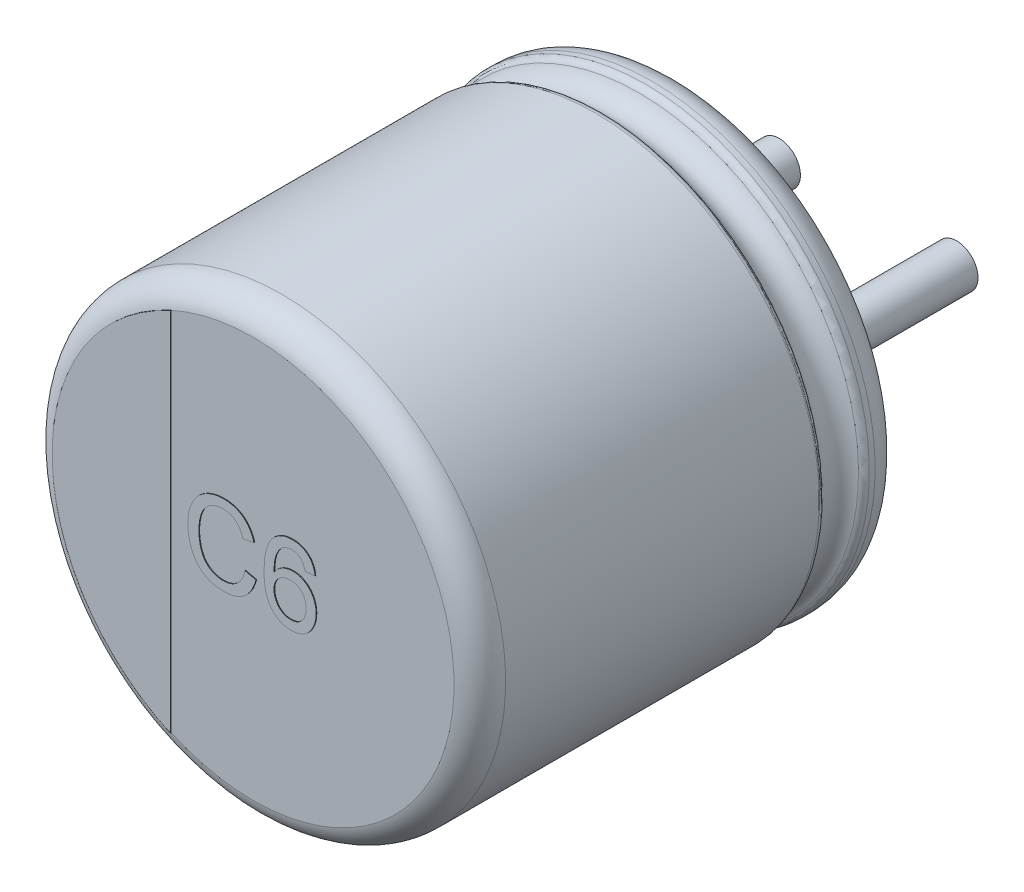
SolidWorks part; units mm, degrees
ref_plane "Plan de face" through (0, 0, 0) normal (0, 0, 1) x (1, 0, 0)
ref_plane "Plan de dessus" through (0, 0, 0) normal (0, 1, 0) x (1, 0, 0)
ref_plane "Plan de droite" through (0, 0, 0) normal (1, 0, 0) x (0, 0, -1)
sketch "Sketch10" plane through (0, 0, 0) normal (1, 0, 0) x (0, 0, -1)
  line L0 (18.1631, 0) -> (-18.9631, 0) construction
  line L1 (-6, 0) -> (-0.05, 0)
  line L2 (-6, 0) -> (-6, 2.8236)
  line L3 (-5.6, 3.15) -> (-1.1846, 3.15)
  line L4 (-0.05, 2.5531) -> (-0.05, 0)
  line L7 (-0.4794, 3.15) -> (-0.3982, 3.15)
  arc A0 (-6, 2.8236) -> (-5.6, 3.15) centre (-5.6068, 2.7501) cw
  arc A1 (-0.3982, 3.15) -> (-0.05, 2.5531) centre (-0.3982, 2.75) cw
  arc A2 (-0.5713, 3.0894) -> (-1.0926, 3.0894) centre (-0.832, 3.201) cw
  arc A3 (-1.0926, 3.0894) -> (-1.1846, 3.15) centre (-1.1846, 3.05) ccw
  arc A4 (-0.5713, 3.0894) -> (-0.4794, 3.15) centre (-0.4794, 3.05) cw
  point P4 (0.57, 0)
  point P13 (-6, 3.15)
  dimension "D2" = 0.4
  dimension "D3" = 0.4
  dimension "D4" = 0.1
  dimension "D5" = 0.1
  dimension "D1" = 3.15
  dimension "D7" = 0.05
  dimension "D8" = 3.15
revolve "Повернуть1" add sketch "Sketch10" angle 360 about L0
sketch "Эскиз2" plane through (0, 0, 0.05) normal (0, 0, -1) x (-1, 0, 0)
  line L1 (0, 0.7993) -> (0, -1.0496) construction
  line L2 (-1.25, 0) -> (3.6313, 0) construction
  circle A3 centre (-1.25, 0) radius 0.3
  circle A7 centre (1.25, 0) radius 0.3
  dimension "D1" = 2.5
extrude "Бобышка-Вытянуть1" add sketch "Эскиз2" along normal blind 2.7
sketch "Эскиз4" plane through (0, 0, 6) normal (0, 0, 1) x (1, 0, 0)
  line L0 (-1.1603, -2.5741) -> (-1.1603, 2.5741)
  circle A1 centre (0, 0) radius 2.8236 construction
  arc A2 (-1.1603, 2.5741) -> (-1.1603, -2.5741) centre (0, 0) ccw
extrude "Бобышка-Вытянуть2" add sketch "Эскиз4" along normal blind 0.01
sketch "Эскиз5" plane through (0, 0, 6) normal (0, 0, 1) x (1, 0, 0)
  text T0 "C6" font "Arial" height 1.1
extrude "Текст" add sketch "Эскиз5" along normal blind 0.01
sketch "Эскиз6" plane through (0, 0, 0.05) normal (0, 0, -1) x (-1, 0, 0)
  line L0 (-1.25, 0.4) -> (-1.6248, 0.4)
  line L1 (-1.25, -0.4) -> (-1.6248, -0.4)
  line L2 (1.25, -0.4) -> (1.6248, -0.4)
  line L3 (1.25, 0.4) -> (1.6248, 0.4)
  arc A0 (-1.8569, -0.7429) -> (1.8569, -0.7429) centre (0, 0) ccw
  arc A1 (-1.25, -0.4) -> (-1.25, 0.4) centre (-1.25, 0) ccw
  arc A2 (1.25, 0.4) -> (1.25, -0.4) centre (1.25, 0) ccw
  arc A3 (1.8569, 0.7429) -> (-1.8569, 0.7429) centre (0, 0) ccw
  arc A4 (1.6248, 0.4) -> (1.8569, 0.7429) centre (1.6248, 0.65) ccw
  arc A5 (1.6248, -0.4) -> (1.8569, -0.7429) centre (1.6248, -0.65) cw
  arc A6 (-1.8569, -0.7429) -> (-1.6248, -0.4) centre (-1.6248, -0.65) cw
  arc A7 (-1.6248, 0.4) -> (-1.8569, 0.7429) centre (-1.6248, 0.65) cw
  point P7 (1.9596, 0.4)
  point P23 (0, -2)
  point P24 (0, 2)
  dimension "D1" = 0.25
  dimension "D2" = 4
extrude "Бобышка-Вытянуть5" add sketch "Эскиз6" along normal blind 0.05 contours A3 A7 L0 A1 L1 A6 A0 A5 L2 A2 L3 A4
